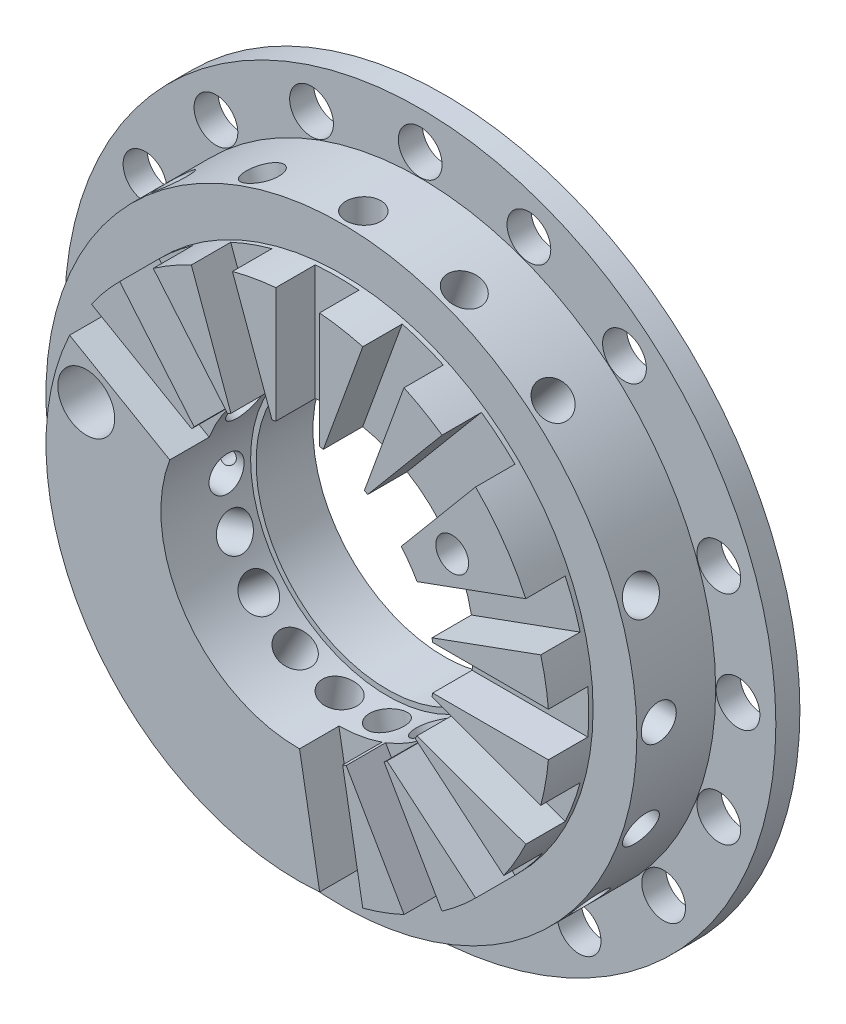
SolidWorks part; units mm, degrees
ref_plane "Front Plane" through (0, 0, 0) normal (0, 0, 1) x (1, 0, 0)
ref_plane "Top Plane" through (0, 0, 0) normal (0, 1, 0) x (1, 0, 0)
ref_plane "Right Plane" through (0, 0, 0) normal (1, 0, 0) x (0, 0, -1)
sketch "Sketch1" plane through (0, 0, 0) normal (0, 0, 1) x (1, 0, 0)
  circle A0 centre (0, 0) radius 16.25
  dimension "D1" = 32.5
extrude "Boss-Extrude1" add sketch "Sketch1" along normal blind 6.7
sketch "Sketch2" plane through (0, 0, 6.7) normal (0, 0, 1) x (1, 0, 0)
  circle A0 centre (0, 0) radius 13.5
  dimension "D1" = 27
extrude "Cut-Extrude1" cut sketch "Sketch2" against normal blind 5.6 flip side to cut
sketch "Sketch3" plane through (0, 0, 6.7) normal (0, 0, 1) x (1, 0, 0)
  circle A0 centre (0, 0) radius 11.5
  dimension "D1" = 23
extrude "Cut-Extrude2" cut sketch "Sketch3" against normal blind 2 flip side to cut
sketch "Sketch4" plane through (0, 0, 6.7) normal (0, 0, 1) x (1, 0, 0)
  circle A0 centre (0, 0) radius 6
  dimension "D1" = 12
extrude "Cut-Extrude3" cut sketch "Sketch4" against normal through all
sketch "Sketch5" plane through (0, 0, 6.7) normal (0, 0, 1) x (1, 0, 0)
  circle A0 centre (0, 0) radius 6.25
  dimension "D1" = 12.5
extrude "Cut-Extrude4" cut sketch "Sketch5" against normal blind 4.1
hole_wizard "Ø2.0 (2) Diameter Hole1" positions "Sketch10" profile "Sketch9" hole size "Ø2.0" standard "DIN" end condition up to next
sketch "Sketch10" plane through (0, 0, 1.1) normal (0, 0, 1) x (1, 0, 0)
  line L0 (0, 0) -> (-14.52, 0) construction
  line L1 (0, 0) -> (-12.5747, 7.26) construction
  line L2 (0, 0) -> (-9.3333, 11.123) construction
  line L3 (-4.9661, 13.6443) -> (0, 0) construction
  line L4 (0, 14.52) -> (0, 0) construction
  line L5 (0, 0) -> (4.9661, 13.6443) construction
  line L6 (9.3333, 11.123) -> (0, 0) construction
  line L7 (0, 0) -> (-13.6443, -4.9661) construction
  line L8 (0, 0) -> (-11.123, -9.3333) construction
  line L9 (0, 0) -> (-7.26, -12.5747) construction
  line L10 (0, 0) -> (-2.5214, -14.2994) construction
  line L11 (0, 0) -> (2.5214, -14.2994) construction
  line L12 (0, 0) -> (7.26, -12.5747) construction
  line L13 (0, 0) -> (11.123, -9.3333) construction
  line L14 (0, 0) -> (14.52, 0) construction
  line L15 (0, 0) -> (13.6443, 4.9661) construction
  line L16 (0, 0) -> (13.6443, -4.9661) construction
  circle A0 centre (0, 0) radius 14.52 construction
  point P15 (-9.3333, 11.123)
  point P16 (-4.9661, 13.6443)
  point P18 (0, 14.52)
  point P22 (4.9661, 13.6443)
  point P23 (9.3333, 11.123)
  point P27 (-13.6443, -4.9661)
  point P29 (-11.123, -9.3333)
  point P31 (-7.26, -12.5747)
  point P33 (-2.5214, -14.2994)
  point P36 (2.5214, -14.2994)
  point P38 (7.26, -12.5747)
  point P40 (11.123, -9.3333)
  point P42 (14.52, 0)
  point P46 (13.6443, 4.9661)
  point P48 (-14.52, 0)
  point P50 (-12.5747, 7.26)
  point P80 (13.6443, -4.9661)
  dimension "D1" = 29.04
  dimension "D2" = 30
  dimension "D3" = 50
  dimension "D4" = 70
  dimension "D5" = 90
  dimension "D6" = 110
  dimension "D7" = 130
  dimension "D8" = 20
  dimension "D9" = 40
  dimension "D10" = 60
  dimension "D11" = 80
  dimension "D12" = 100
  dimension "D13" = 120
  dimension "D14" = 140
  dimension "D15" = 200
  dimension "D16" = 160
sketch "Sketch9" plane through (-9.3333, 11.123, 1.1) normal (1, 0, 0) x (0, -1, 0)
  line L0 (0, 0) -> (0, 1.1)
  line L1 (0, 1.1) -> (1, 1.1)
  line L2 (1, 1.1) -> (1, 0)
  line L5 (1, 0) -> (0, 0)
  line L11 (0, -6.35) -> (0, 107.95) construction
  dimension "Thru Hole Dia." = 2
  dimension "Thru Hole Depth" = 1.1
sketch "Sketch11" plane through (0, 0, 6.7) normal (0, 0, 1) x (1, 0, 0)
  line L2 (0.5, 0.866) -> (-12.0747, 8.126)
  line L3 (-4.8429, 3.9508) -> (-9.4216, 6.5942)
  line L4 (-0.5, -0.866) -> (-13.0747, 6.394)
  line L5 (-5.8429, 2.2187) -> (-10.4216, 4.8622)
  circle A0 centre (0, 0) radius 6.25 construction
  arc A1 (-4.8429, 3.9508) -> (-5.8429, 2.2187) centre (0, 0) ccw
  circle A2 centre (0, 0) radius 11.5 construction
  arc A3 (-9.4216, 6.5942) -> (-10.4216, 4.8622) centre (0, 0) ccw
  dimension "D1" = 1
  dimension "D2" = 1
extrude "Cut-Extrude5" cut sketch "Sketch11" against normal blind 1.8
pattern_circular "CirPattern1" count 6 every 20 about axis through (0, 0, 0) along (0, 0, 1) of "Cut-Extrude5"
sketch "Sketch12" plane through (0, 0, 6.7) normal (0, 0, 1) x (1, 0, 0)
  line L2 (0.342, -0.9397) -> (13.9864, 4.0264)
  line L3 (6.1394, 1.1704) -> (11.1076, 2.9786)
  line L4 (-0.342, 0.9397) -> (13.3023, 5.9058)
  line L5 (5.4554, 3.0498) -> (10.4235, 4.858)
  arc A0 (-10.4216, 4.8622) -> (8.1301, 8.1334) centre (0, 0) ccw construction
  arc A1 (11.1076, 2.9786) -> (10.4235, 4.858) centre (0, 0) ccw
  arc A2 (-5.8429, 2.2187) -> (4.7317, 4.0833) centre (0, 0) ccw construction
  arc A3 (6.1394, 1.1704) -> (5.4554, 3.0498) centre (0, 0) ccw
  dimension "D1" = 1
  dimension "D2" = 1
extrude "Cut-Extrude6" cut sketch "Sketch12" against normal up to surface (1.8 mm away) up to face at (5.6848, 6.7749, 4.9)
pattern_circular "CirPattern2" count 6 every 20 about axis through (0, 0, 0) along (0, 0, 1) of "Cut-Extrude6"
sketch "Sketch13" plane through (0, 0, 4.7) normal (0, 0, 1) x (1, 0, 0)
  line L0 (0, 0) -> (-14.52, 0) construction
  line L1 (0, 0) -> (-12.5747, 7.26) construction
  line L2 (0, 0) -> (-13.5, 0) construction
  line L3 (0, 0) -> (-11.6913, 6.75) construction
  circle A0 centre (0, 0) radius 13.5 construction
ref_plane "Plane1" through (-13.5, 0, 4.7) normal (-1, 0, 0) x (0, 0, 1)
hole_wizard "Ø1.6 (1.6) Diameter Hole1" positions "Sketch15" profile "Sketch14" hole size "Ø1.6" standard "DIN"
sketch "Sketch15" plane through (-13.5, 0, 4.7) normal (-1, 0, 0) x (0, 0, 1)
  line L0 (2, -11.5) -> (2, 4.8622) construction
  line L1 (0.2, 0) -> (2, 0) construction
  point P0 (-1, 0)
  dimension "D1" = 3
sketch "Sketch14" plane through (-13.5, 0, 3.7) normal (0, 1, 0) x (0, 0, 1)
  line L0 (0, 0) -> (0, 21.512)
  line L1 (0, 21.512) -> (0.8, 21.512)
  line L2 (0.8, 21.512) -> (0.8, 0)
  line L5 (0.8, 0) -> (0, 0)
  line L11 (0, -6.35) -> (0, 107.95) construction
  dimension "Thru Hole Dia." = 1.6
  dimension "Thru Hole Depth" = 21.512
pattern_circular "CirPattern3" count 11 every 20 about axis through (0, 0, 4.7) along (0, 0, 1) of "Ø1.6 (1.6) Diameter Hole1"
ref_plane "Plane2" through (-11.6913, 6.75, 4.7) normal (-0.866, 0.5, 0) x (0, 0, 1)
hole_wizard "Ø1.6 (1.6) Diameter Hole2" positions "Sketch17" profile "Sketch16" hole size "Ø1.6" standard "DIN"
sketch "Sketch17" plane through (-11.6913, 6.75, 4.7) normal (-0.866, 0.5, 0) x (0, 0, 1)
  line L0 (-3.6, 0) -> (0, 0) construction
  line L1 (0.2, 0) -> (2, 0) construction
  line L3 (2, -11.5) -> (2, -1) construction
  point P0 (-1, 0)
  dimension "D1" = 3
sketch "Sketch16" plane through (-11.6913, 6.75, 3.7) normal (0, 0, 1) x (-0.5, -0.866, 0)
  line L0 (0, 0) -> (0, 27)
  line L1 (0, 27) -> (0.8, 27)
  line L2 (0.8, 27) -> (0.8, 0)
  line L5 (0.8, 0) -> (0, 0)
  line L11 (0, -6.35) -> (0, 107.95) construction
  dimension "Thru Hole Dia." = 1.6
  dimension "Thru Hole Depth" = 27
pattern_circular "CirPattern4" count 6 every 20 about axis through (0, 0, 4.7) along (0, 0, 1) of "Ø1.6 (1.6) Diameter Hole2"
hole_wizard "Ø2.6 (2.6) Diameter Hole1" positions "Sketch19" profile "Sketch18" hole size "Ø2.6" standard "DIN" end condition up to next
sketch "Sketch19" plane through (0, 0, 6.7) normal (0, 0, 1) x (1, 0, 0)
  line L0 (0, 0) -> (-10, 0) construction
  line L1 (0, 0) -> (-9.6593, 2.5882) construction
  circle A0 centre (0, 0) radius 10 construction
  point P8 (-9.6593, 2.5882)
  dimension "D1" = 20
  dimension "D2" = 15
sketch "Sketch18" plane through (-9.6593, 2.5882, 6.7) normal (1, 0, 0) x (0, -1, 0)
  line L0 (0, 0) -> (0, 6.7)
  line L1 (0, 6.7) -> (1.3, 6.7)
  line L2 (1.3, 6.7) -> (1.3, 0)
  line L5 (1.3, 0) -> (0, 0)
  line L11 (0, -6.35) -> (0, 107.95) construction
  dimension "Thru Hole Dia." = 2.6
  dimension "Thru Hole Depth" = 6.7
hole_wizard "Ø1.5 (1.5) Diameter Hole1" positions "Sketch21" profile "Sketch20" hole size "Ø1.5" standard "DIN" end condition up to next
sketch "Sketch21" plane through (0, 0, 6.7) normal (0, 0, 1) x (1, 0, 0)
  line L0 (0, 0) -> (8.62, 0) construction
  line L1 (0, 0) -> (7.0611, 4.9442) construction
  circle A0 centre (0, 0) radius 8.62 construction
  point P7 (7.0611, 4.9442)
  dimension "D1" = 17.24
  dimension "D2" = 35
sketch "Sketch20" plane through (7.0611, 4.9442, 6.7) normal (1, 0, 0) x (0, -1, 0)
  line L0 (0, 0) -> (0, 6.7)
  line L1 (0, 6.7) -> (0.75, 6.7)
  line L2 (0.75, 6.7) -> (0.75, 0)
  line L5 (0.75, 0) -> (0, 0)
  line L11 (0, -6.35) -> (0, 107.95) construction
  dimension "Thru Hole Dia." = 1.5
  dimension "Thru Hole Depth" = 6.7
hole_wizard "Ø0.8 (0.8) Diameter Hole1" positions "Sketch23" profile "Sketch22" hole size "Ø0.8" standard "DIN"
sketch "Sketch23" plane through (0, 0, 0) normal (0, 0, -1) x (-1, 0, 0)
  circle A0 centre (0, 0) radius 7 construction
  point P7 (-7, 0)
  point P9 (7, 0)
  dimension "D1" = 14
sketch "Sketch22" plane through (7, 0, 0) normal (1, 0, 0) x (0, 1, 0)
  line L0 (0, 0) -> (0, 2.9)
  line L1 (0, 2.9) -> (0.4, 2.9)
  line L2 (0.4, 2.9) -> (0.4, 0)
  line L5 (0.4, 0) -> (0, 0)
  line L11 (0, -6.35) -> (0, 107.95) construction
  dimension "Thru Hole Dia." = 0.8
  dimension "Thru Hole Depth" = 2.9
